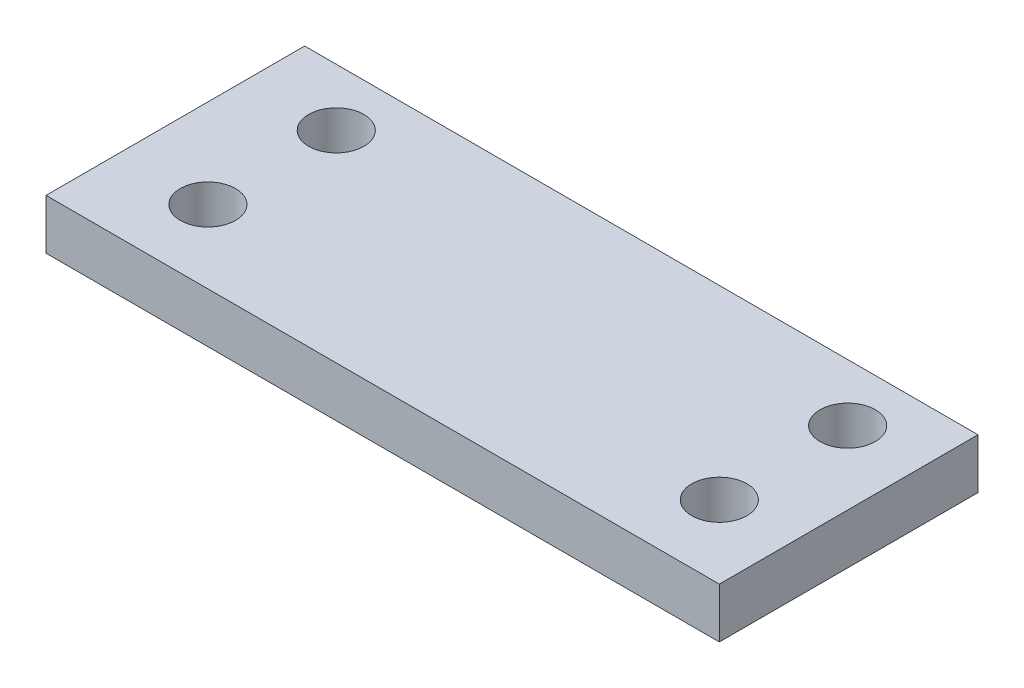
SolidWorks part; units mm, degrees
ref_plane "Front Plane" through (0, 0, 0) normal (0, 0, 1) x (1, 0, 0)
ref_plane "Top Plane" through (0, 0, 0) normal (0, 1, 0) x (1, 0, 0)
ref_plane "Right Plane" through (0, 0, 0) normal (1, 0, 0) x (0, 0, -1)
sketch "Sketch2" plane through (0, 0, 0) normal (0, 1, 0) x (1, 0, 0)
  line L1 (60.6688, 31.7132) -> (-73.6692, 31.7132)
  line L2 (60.6688, 31.7132) -> (60.6688, -19.8946)
  line L3 (60.6688, -19.8946) -> (-73.6692, -19.8946)
  line L4 (-73.6692, 31.7132) -> (-73.6692, -19.8946)
  circle A0 centre (-55.9414, 20.2886) radius 5.5153
  circle A1 centre (-55.9414, -5.3184) radius 5.5153
  circle A2 centre (46.0925, -5.3184) radius 5.5153
  circle A3 centre (46.0925, 20.2886) radius 5.5153
extrude "Boss-Extrude1" add sketch "Sketch2" along normal blind 10
